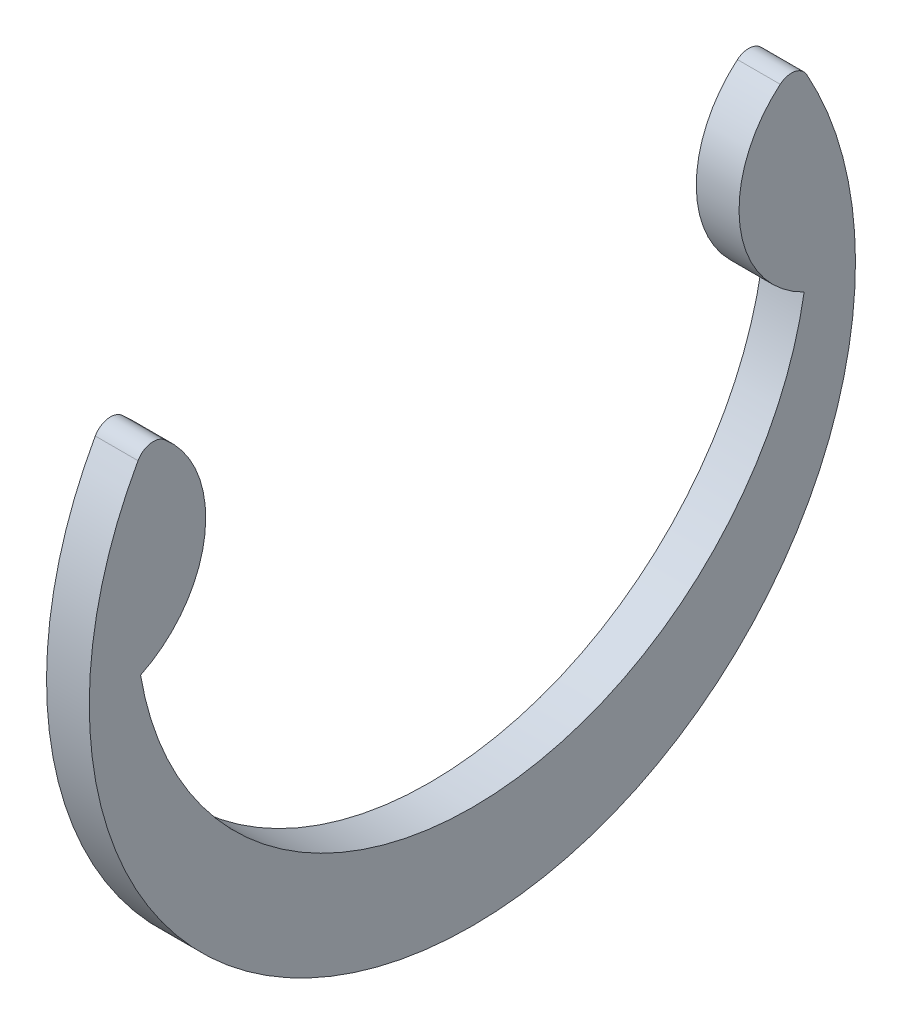
SolidWorks part; units mm, degrees
material "Cast Carbon Steel"
ref_plane "Front" through (0, 0, 0) normal (0, 0, 1) x (1, 0, 0)
ref_plane "Top" through (0, 0, 0) normal (0, 1, 0) x (1, 0, 0)
ref_plane "Right" through (0, 0, 0) normal (1, 0, 0) x (0, 0, -1)
sketch "Sketch1" plane through (0, 0, 0) normal (1, 0, 0) x (0, 0, -1)
  circle A0 centre (0, 0) radius 4.1656 construction
  arc A1 (-4.9276, 0) -> (4.9276, 0) centre (0, 0.8317) ccw
  circle A2 centre (0, 0) radius 5.6896 construction
  circle A3 centre (0, 0) radius 5.969 construction
  arc A4 (4.9658, 2.7771) -> (-4.9658, 2.7771) centre (0, 0) cw
  arc A5 (-4.5718, 2.8495) -> (-4.9276, 0) centre (-5.6691, 1.5395) cw
  arc A6 (-4.9658, 2.7771) -> (-4.5718, 2.8495) centre (-4.7388, 2.6501) cw
  arc A7 (4.9658, 2.7771) -> (4.5718, 2.8495) centre (4.7388, 2.6501) ccw
  arc A8 (4.9276, 0) -> (4.5718, 2.8495) centre (5.6691, 1.5395) cw
  arc A9 (4.5718, 2.8495) -> (4.9276, 0) centre (0, 0.8317) cw construction
  dimension "D1" = 2.7771
  dimension "A" = 8.3312
  dimension "D2" = 9.8552
  dimension "L" = 11.938
  dimension "OD" = 11.3792
extrude "Extrude1" add sketch "Sketch1" along normal mid plane 0.635
sketch "Sketch2" plane through (0, 0, 0) normal (0, 0, 1) x (1, 0, 0)
  line L0 (-1.8415, 0) -> (5.5245, 0)
  line L1 (5.5245, 0) -> (5.5245, -4.7625)
  line L3 (5.5245, -4.7625) -> (0.3683, -4.7625)
  line L4 (0.3683, -4.7625) -> (0.3683, -4.2545)
  line L5 (0.3683, -4.2545) -> (-0.3683, -4.2545)
  line L6 (-0.3683, -4.2545) -> (-0.3683, -4.7625)
  line L7 (-0.3683, -4.7625) -> (-1.8415, -4.7625) construction
  line L8 (-1.8415, -4.7625) -> (-1.8415, 0) construction
  line L9 (0, -4.2545) -> (0, 0) construction
  line L10 (5.5245, 0) -> (14.0551, 0) construction
  line L11 (-0.3683, -4.7625) -> (-1.5875, -4.7625)
  line L12 (-1.5875, -4.7625) -> (-1.8415, -4.5085)
  line L13 (-1.8415, -4.5085) -> (-1.8415, 0)
  point P14 (-0.3683, -4.5085)
  dimension "Dg" = 8.509
  dimension "Ds" = 9.525
  dimension "D2" = 7.366
  dimension "W" = 0.7366
  dimension "D3" = 1.8415
  dimension "D4" = 45
revolve "Revolve1" [suppressed] add sketch "Sketch2" angle 360 about L10
equation "\"D2@Sketch2\" = \"W@Sketch2\"*10"
equation "\"D3@Sketch2\" = \"D2@Sketch2\"/4"
equation "\"D1@Sketch1\" = \"A@Sketch1\"/3"
equation "\"D2@Sketch1\" = (\"OD@Sketch1\"+\"A@Sketch1\")/2"
